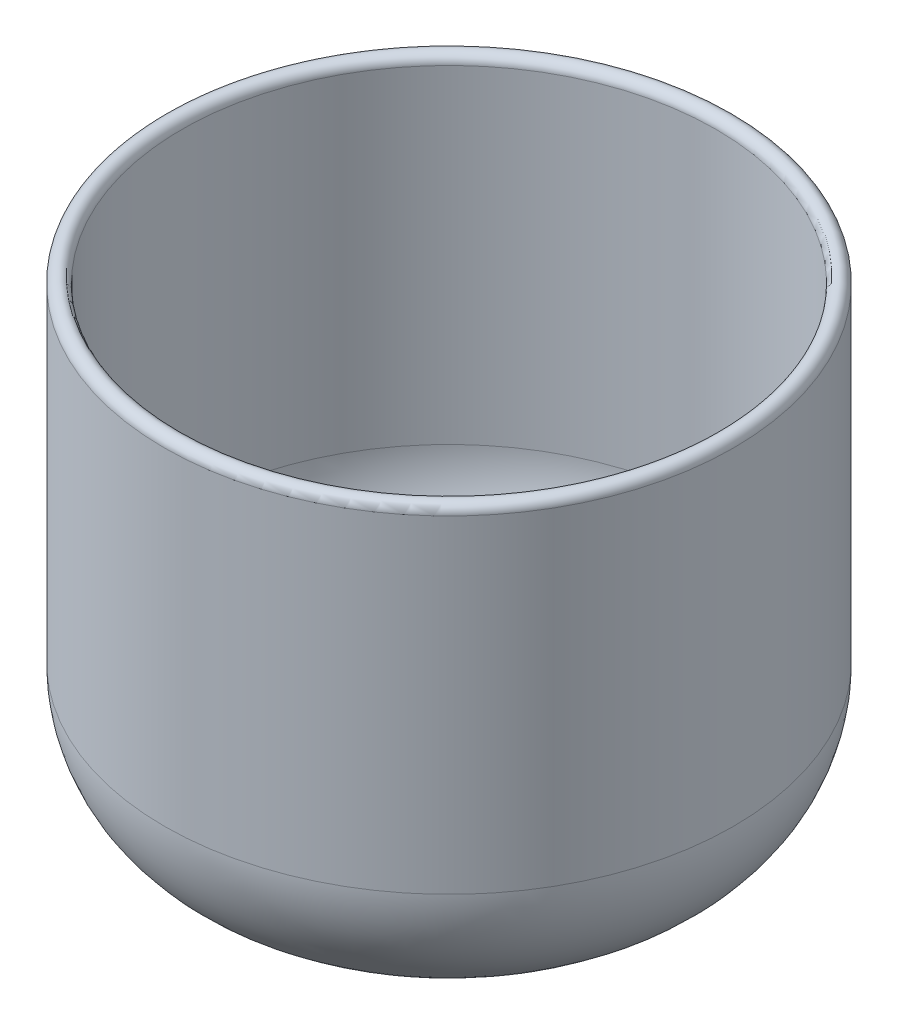
SolidWorks part; units mm, degrees
ref_plane "Front Plane" through (0, 0, 0) normal (0, 0, 1) x (1, 0, 0)
ref_plane "Top Plane" through (0, 0, 0) normal (0, 1, 0) x (1, 0, 0)
ref_plane "Right Plane" through (0, 0, 0) normal (1, 0, 0) x (0, 0, -1)
sketch "Sketch1" plane through (0, 0, 0) normal (0, 0, 1) x (1, 0, 0)
  line L0 (0, 0) -> (0, 95.564) construction
  line L1 (0, 0) -> (12.7, 0)
  line L2 (40.0051, 68.6292) -> (0, 68.6292) construction
  line L3 (24.6239, 1.0854) -> (0, 1.0854) construction
  line L4 (41.275, 21.0714) -> (0, 21.0714) construction
  line L5 (0, 2.54) -> (12.7, 2.54)
  line L6 (0, 2.54) -> (0, 0)
  line L7 (41.275, 21.0714) -> (41.275, 97.3158) construction
  line L8 (38.7349, 21.023) -> (38.7349, 68.6292)
  line L9 (41.275, 21.0714) -> (41.275, 68.6026)
  arc A0 (12.7, 0) -> (24.6239, 1.0854) centre (12.7, 66.04) ccw
  arc A1 (24.6239, 1.0854) -> (41.275, 21.0714) centre (20.955, 21.0714) ccw
  arc A2 (38.7349, 68.6292) -> (41.275, 68.6026) centre (40.0051, 68.6292) cw
  arc A4 (24.1653, 3.5836) -> (38.7349, 21.023) centre (20.955, 21.0714) ccw
  arc A5 (12.7, 2.54) -> (24.1653, 3.5836) centre (12.7, 66.04) ccw
  arc A7 (34.271, 68.58) -> (41.275, 21.0714) centre (-183.2053, 12.2478) cw construction
  arc A8 (31.8122, 67.9431) -> (38.7349, 21.023) centre (-183.2053, 12.2478) cw construction
  dimension "D4" = 66.04
  dimension "D6" = 20.32
  dimension "D1" = 68.6292
  dimension "D2" = 12.7
  dimension "D9" = 41.275
  dimension "D8" = 2.54
revolve "Revolve1" add sketch "Sketch1" angle 360 about L0
